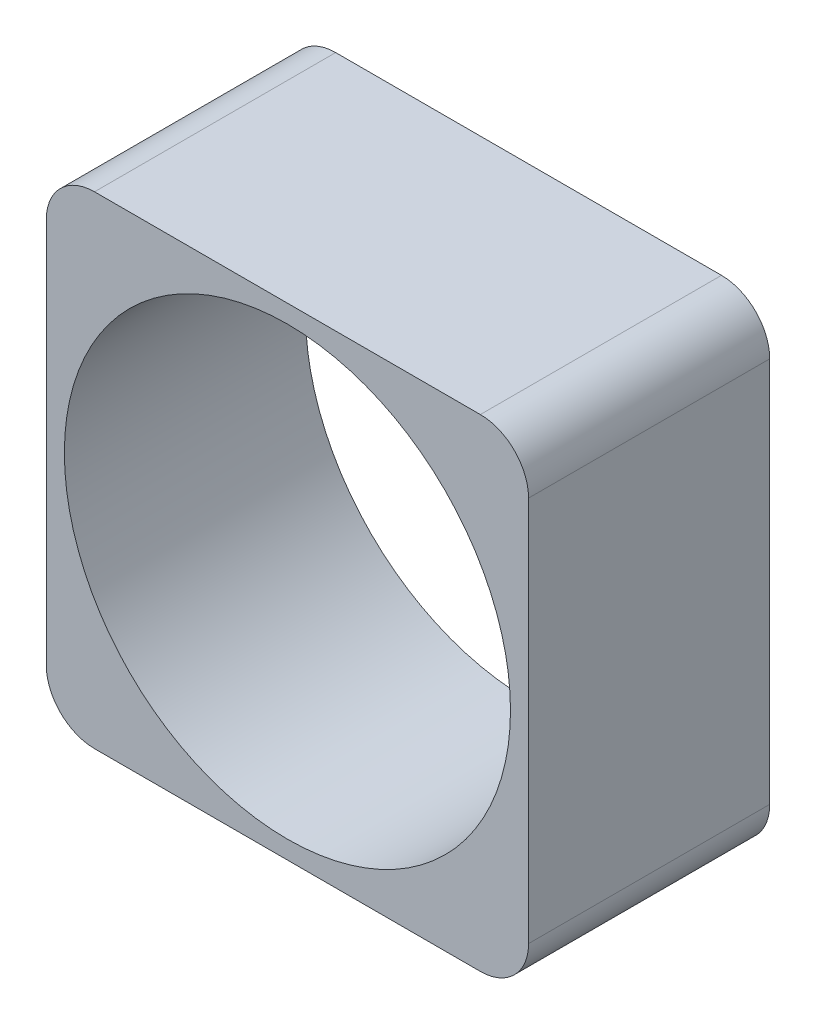
SolidWorks part; units mm, degrees
ref_plane "Piano frontale" through (0, 0, 0) normal (0, 0, 1) x (1, 0, 0)
ref_plane "Piano superiore" through (0, 0, 0) normal (0, 1, 0) x (1, 0, 0)
ref_plane "Piano destro" through (0, 0, 0) normal (1, 0, 0) x (0, 0, -1)
sketch "Schizzo1" plane through (0, 0, 0) normal (0, 0, 1) x (1, 0, 0)
  line L1 (16, -20) -> (-16, -20)
  line L2 (20, -16) -> (20, 16)
  line L3 (16, 20) -> (-16, 20)
  line L4 (-20, -16) -> (-20, 16)
  line L5 (20, -20) -> (-20, 20) construction
  line L6 (20, 20) -> (-20, -20) construction
  arc A0 (-20, -16) -> (-16, -20) centre (-16, -16) ccw
  arc A1 (16, -20) -> (20, -16) centre (16, -16) ccw
  arc A2 (20, 16) -> (16, 20) centre (16, 16) ccw
  arc A3 (-16, 20) -> (-20, 16) centre (-16, 16) ccw
  point P0 (0, 0)
  dimension "D3" = 4
  dimension "D1" = 40
  dimension "D2" = 40
extrude "Estrusione-Estrusione1" add sketch "Schizzo1" along normal blind 20
sketch "Schizzo2" plane through (0, 0, 20) normal (0, 0, 1) x (1, 0, 0)
  circle A0 centre (0, 0) radius 18.5
  dimension "D1" = 37
extrude "Taglio-Estrusione1" cut sketch "Schizzo2" against normal blind 20
